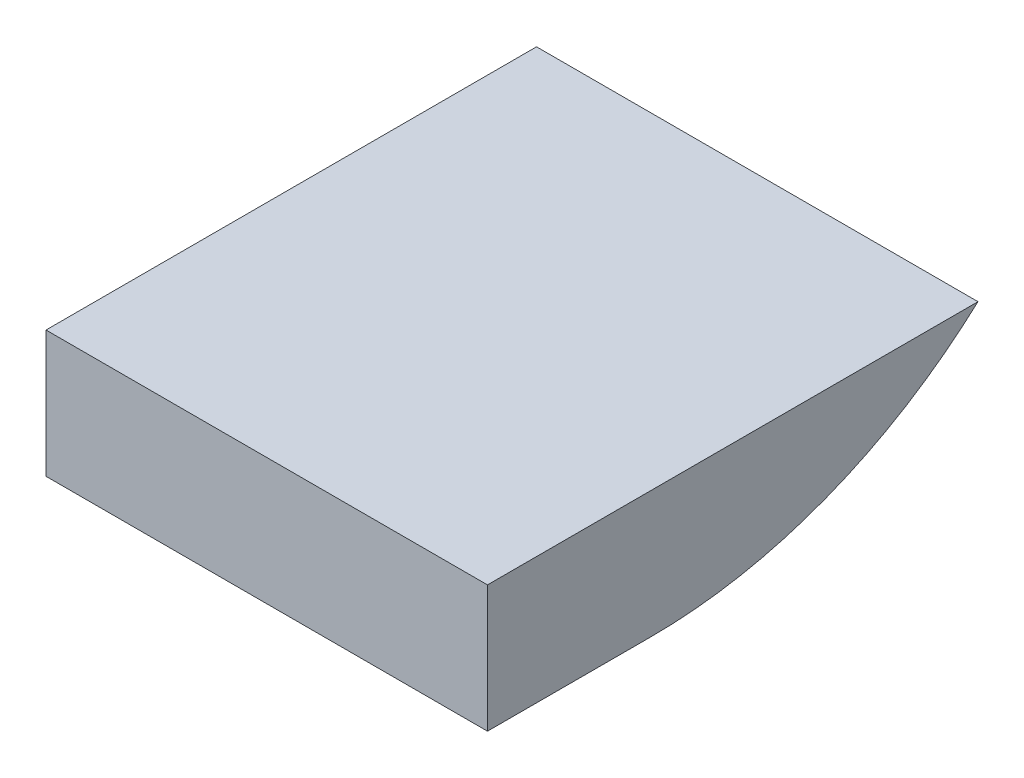
SolidWorks part; units mm, degrees
ref_plane "Front Plane" through (0, 0, 0) normal (0, 0, 1) x (1, 0, 0)
ref_plane "Top Plane" through (0, 0, 0) normal (0, 1, 0) x (1, 0, 0)
ref_plane "Right Plane" through (0, 0, 0) normal (1, 0, 0) x (0, 0, -1)
sketch "Sketch3" plane through (0, 0, 0) normal (1, 0, 0) x (0, 0, -1)
  line L0 (0, -1.55) -> (2, -1.55)
  line L1 (-2, 1.55) -> (10, 1.55)
  line L2 (-2, 1.55) -> (-2, -1.55)
  line L3 (-2, -1.55) -> (2, -1.55)
  arc A0 (2, -1.55) -> (10, 1.55) centre (2, 10.3226) ccw
  point P4 (-2, 0)
  dimension "D1" = 3.1
  dimension "D2" = 2
  dimension "D3" = 12
extrude "Boss-Extrude1" add sketch "Sketch3" along normal blind 10.8 contours L0 A0 L1 L2 L3
